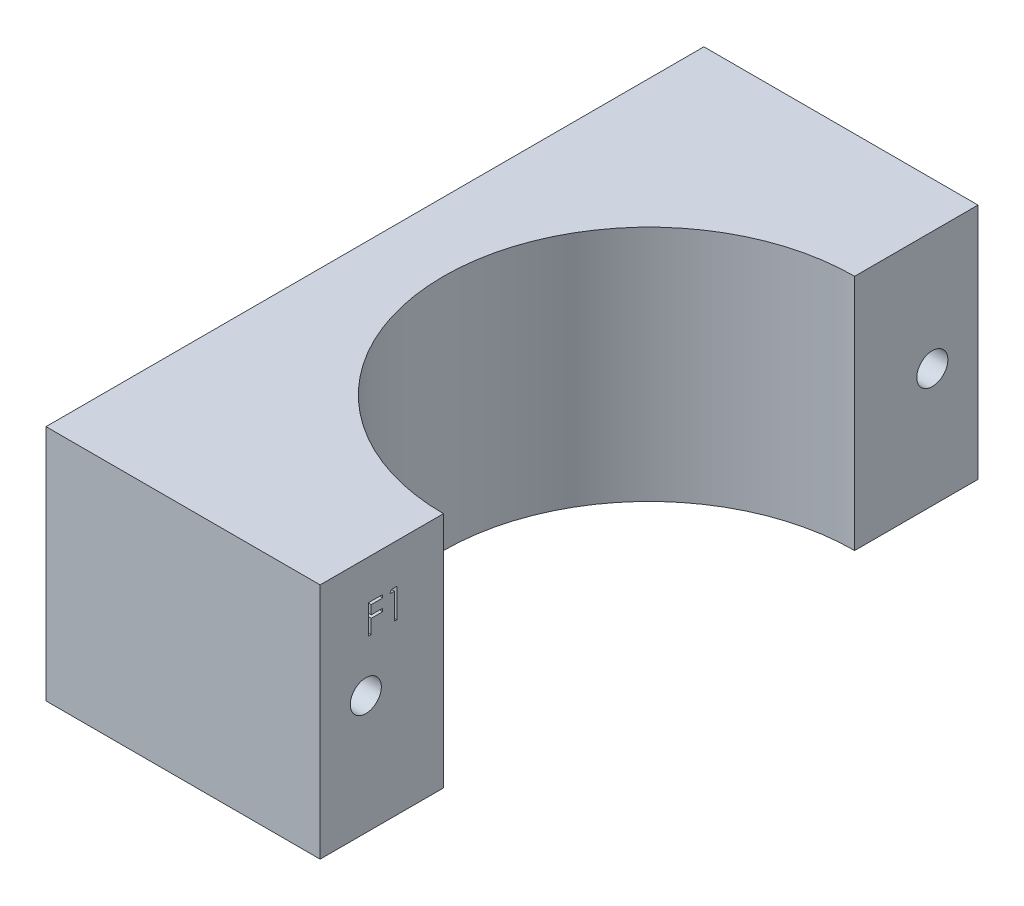
SolidWorks part; units mm, degrees
ref_plane "Front Plane" through (0, 0, 0) normal (0, 0, 1) x (1, 0, 0)
ref_plane "Top Plane" through (0, 0, 0) normal (0, 1, 0) x (1, 0, 0)
ref_plane "Right Plane" through (0, 0, 0) normal (1, 0, 0) x (0, 0, -1)
sketch "Sketch1" plane through (0, 0, 0) normal (0, 1, 0) x (1, 0, 0)
  line L0 (-46.9983, 32.5286) -> (-46.9983, -39.4714)
  line L1 (-46.9983, -39.4714) -> (-16.9983, -39.4714)
  line L2 (-16.9983, -39.4714) -> (-16.9983, -25.9714)
  line L3 (-46.9983, 32.5286) -> (-16.9983, 32.5286)
  line L4 (-16.9983, 32.5286) -> (-16.9983, 19.0286)
  arc A0 (-16.9983, 19.0286) -> (-16.9983, -25.9714) centre (-16.9983, -3.4714) ccw
  dimension "D1" = 72
  dimension "D2" = 30
  dimension "D3" = 30
  dimension "D4" = 13.5
  dimension "D5" = 13.5
extrude "Boss-Extrude1" add sketch "Sketch1" along normal blind 26
sketch "Sketch2" plane through (-16.9983, 0, 0) normal (1, 0, 0) x (0, 0, -1)
  line L0 (-34.4714, 26) -> (-34.4714, 0) construction
  line L1 (-39.4714, 26) -> (-25.9714, 26) construction
  line L2 (-39.4714, 0) -> (-25.9714, 0) construction
  line L3 (27.5286, 26) -> (27.5286, 0) construction
  line L4 (19.0286, 26) -> (32.5286, 26) construction
  line L5 (19.0286, 0) -> (32.5286, 0) construction
  line L6 (-39.4714, 26) -> (-39.4714, 0) construction
  line L7 (32.5286, 26) -> (32.5286, 0) construction
  circle A0 centre (-34.4714, 13) radius 1.7
  circle A1 centre (27.5286, 13) radius 1.7
  dimension "D1" = 5
  dimension "D2" = 5
extrude "Cut-Extrude1" cut sketch "Sketch2" against normal through all
sketch "Sketch3" plane through (-16.9983, 0, 0) normal (1, 0, 0) x (0, 0, -1)
  text T0 "F1"
extrude "Cut-Extrude2" cut sketch "Sketch3" against normal blind 1
